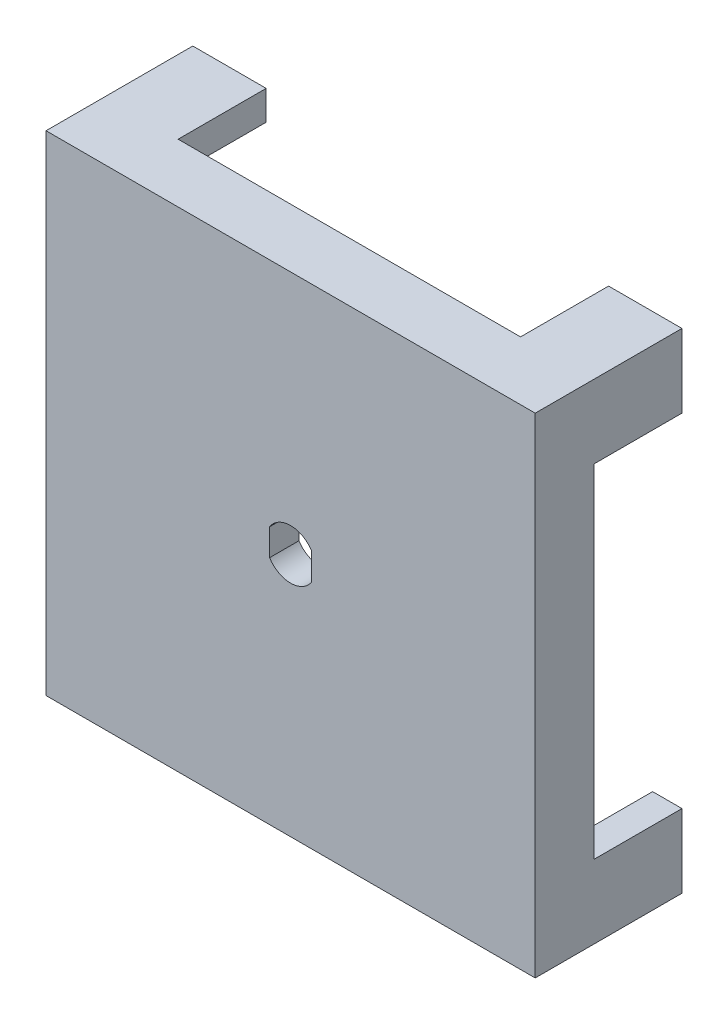
SolidWorks part; units mm, degrees
ref_plane "Front Plane" through (0, 0, 0) normal (0, 0, 1) x (1, 0, 0)
ref_plane "Top Plane" through (0, 0, 0) normal (0, 1, 0) x (1, 0, 0)
ref_plane "Right Plane" through (0, 0, 0) normal (1, 0, 0) x (0, 0, -1)
sketch "Sketch1" plane through (0, 0, 0) normal (0, 0, 1) x (1, 0, 0)
  line L1 (-25, -25) -> (25, -25)
  line L2 (-25, -25) -> (-25, 25)
  line L3 (-25, 25) -> (25, 25)
  line L4 (25, -25) -> (25, 25)
  line L5 (-25, -25) -> (25, 25) construction
  line L6 (-25, 25) -> (25, -25) construction
  point P0 (0, 0)
  dimension "D1" = 50
  dimension "D2" = 50
extrude "Boss-Extrude1" add sketch "Sketch1" along normal blind 15
shell "Shell1" thickness 3
sketch "Sketch2" plane through (0, 0, 0) normal (0, 0, -1) x (-1, 0, 0)
  line L0 (0, 2.55) -> (0, -2.55) construction
  line L1 (-2.15, 1.3711) -> (-2.15, -1.3711)
  line L2 (2.15, 1.3711) -> (2.15, -1.3711)
  arc A0 (-2.15, -1.3711) -> (2.15, -1.3711) centre (0, 0) ccw
  arc A1 (-2.15, 1.3711) -> (-2.15, -1.3711) centre (0, 0) ccw construction
  arc A2 (2.15, 1.3711) -> (-2.15, 1.3711) centre (0, 0) ccw
  arc A3 (2.15, -1.3711) -> (2.15, 1.3711) centre (0, 0) ccw construction
  dimension "D1" = 5.1
  dimension "D2" = 2.15
extrude "Cut-Extrude1" cut sketch "Sketch2" against normal through all both and the other way through all
sketch "Sketch4" plane through (0, 0, 0) normal (0, 0, -1) x (-1, 0, 0)
  line L0 (-17.5, 17.5) -> (-17.5, 27.9484)
  line L1 (26.9415, -17.5) -> (17.5, -17.5)
  line L2 (26.9415, -17.5) -> (26.9415, 17.5)
  line L3 (26.9415, 17.5) -> (17.5, 17.5)
  line L4 (-26.9415, -17.5) -> (-26.9415, 17.5)
  line L5 (26.9415, -17.5) -> (-26.9415, 17.5) construction
  line L6 (26.9415, 17.5) -> (-26.9415, -17.5) construction
  line L7 (17.5, -27.9484) -> (-17.5, -27.9484)
  line L8 (17.5, -27.9484) -> (17.5, -17.5)
  line L9 (17.5, 27.9484) -> (-17.5, 27.9484)
  line L10 (-17.5, -27.9484) -> (-17.5, -17.5)
  line L11 (17.5, -27.9484) -> (-17.5, 27.9484) construction
  line L12 (17.5, 27.9484) -> (-17.5, -27.9484) construction
  line L13 (-17.5, 11.3672) -> (-17.5, 17.5) construction
  line L14 (-17.5, -11.3672) -> (-17.5, 11.3672) construction
  line L15 (-17.5, -17.5) -> (-17.5, -11.3672) construction
  line L16 (-17.5, -17.5) -> (-26.9415, -17.5)
  line L17 (-10.9577, -17.5) -> (-17.5, -17.5) construction
  line L18 (10.9577, -17.5) -> (-10.9577, -17.5) construction
  line L19 (17.5, -17.5) -> (10.9577, -17.5) construction
  line L20 (17.5, 17.5) -> (17.5, 27.9484)
  line L21 (17.5, -17.5) -> (17.5, -11.3672) construction
  line L22 (17.5, -11.3672) -> (17.5, 11.3672) construction
  line L23 (17.5, 11.3672) -> (17.5, 17.5) construction
  line L24 (-17.5, 17.5) -> (-26.9415, 17.5)
  line L25 (17.5, 17.5) -> (10.9577, 17.5) construction
  line L26 (10.9577, 17.5) -> (-10.9577, 17.5) construction
  line L27 (-10.9577, 17.5) -> (-17.5, 17.5) construction
  point P0 (0, 0)
  point P6 (0, 0)
  dimension "D1" = 35
  dimension "D2" = 35
extrude "Cut-Extrude2" cut sketch "Sketch4" against normal blind 9
